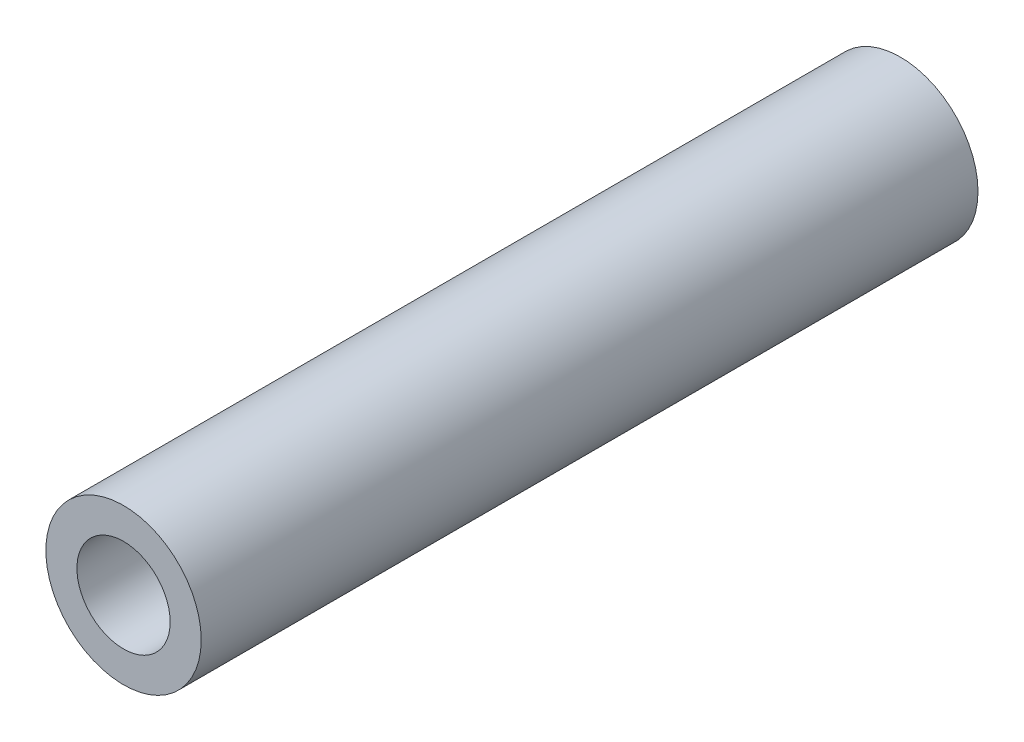
SolidWorks part; units mm, degrees
ref_plane "前视基准面" through (0, 0, 0) normal (0, 0, 1) x (1, 0, 0)
ref_plane "上视基准面" through (0, 0, 0) normal (0, 1, 0) x (1, 0, 0)
ref_plane "右视基准面" through (0, 0, 0) normal (1, 0, 0) x (0, 0, -1)
sketch "草图1" plane through (0, 0, 0) normal (0, 0, 1) x (1, 0, 0)
  circle A0 centre (0, 0) radius 2.5
  circle A1 centre (0, 0) radius 1.5
  dimension "D1" = 3
  dimension "D2" = 5
extrude "凸台-拉伸1" add sketch "草图1" along normal mid plane 25
